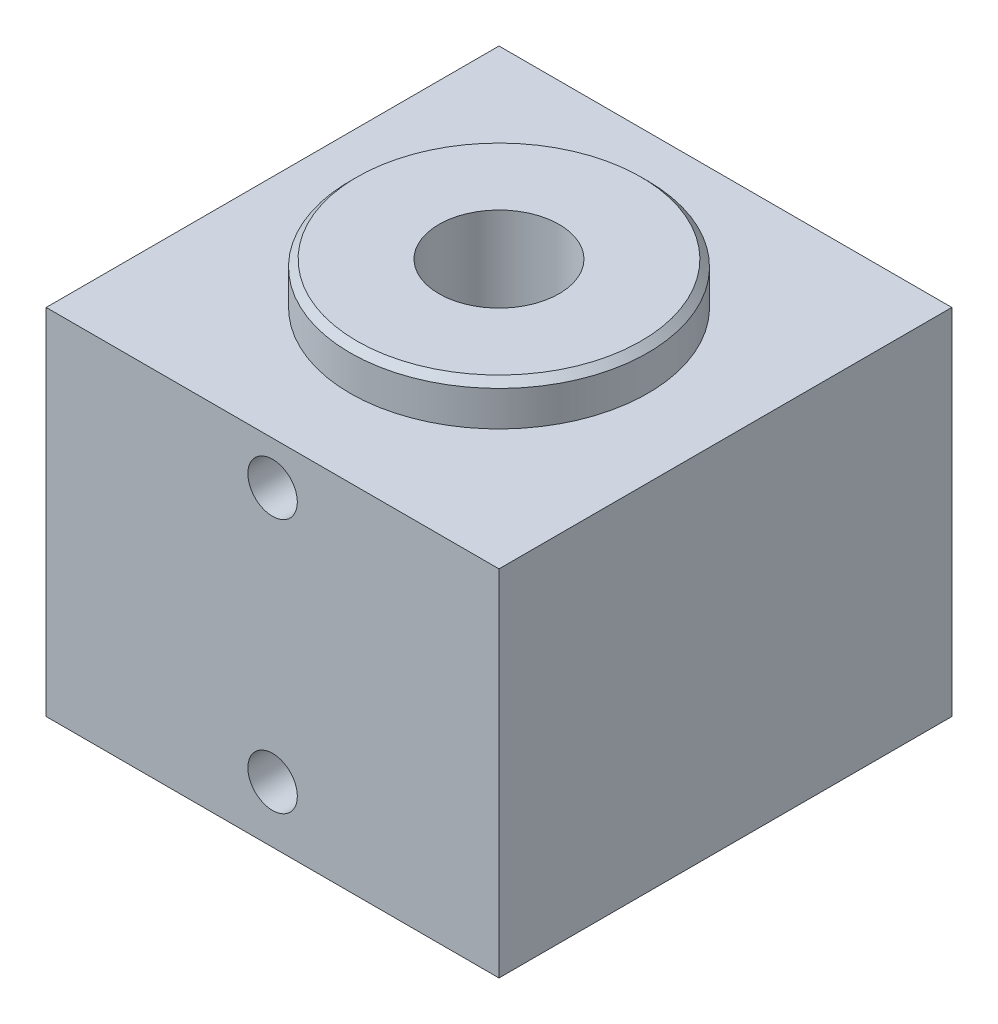
SolidWorks part; units mm, degrees
material "Alloy Steel"
ref_plane "Front Plane" through (0, 0, 0) normal (0, 0, 1) x (1, 0, 0)
ref_plane "Top Plane" through (0, 0, 0) normal (0, 1, 0) x (1, 0, 0)
ref_plane "Right Plane" through (0, 0, 0) normal (1, 0, 0) x (0, 0, -1)
sketch "Sketch1" plane through (0, 0, 0) normal (0, 1, 0) x (1, 0, 0)
  line L0 (-50.8, -50.8) -> (50.8, -50.8)
  line L1 (50.8, -50.8) -> (50.8, 50.8)
  line L2 (50.8, 50.8) -> (-50.8, 50.8)
  line L3 (-50.8, 50.8) -> (-50.8, -50.8)
  line L4 (-55.88, 0) -> (55.88, 0) construction
  line L5 (0, 0.7573) -> (0, -54.4639) construction
  dimension "D1" = 101.6
  dimension "D2" = 50.8
  dimension "D3" = 101.6
extrude "Extrude1" add sketch "Sketch1" along normal blind 79.502
sketch "Sketch2" plane through (0, 79.502, 0) normal (0, 1, 0) x (-1, 0, 0)
  circle A0 centre (0, 0) radius 33.401
  dimension "D1" = 66.802
extrude "Extrude2" add sketch "Sketch2" along normal blind 9.398
chamfer "Chamfer1" distance 1.524 angle 45 1 edges at (0, 88.9, 33.401)
sketch "Sketch3" plane through (0, 88.9, 0) normal (0, 1, 0) x (1, 0, 0)
  circle A0 centre (0, 0) radius 13.4874
  dimension "D1" = 26.9748
extrude "Cut-Extrude1" cut sketch "Sketch3" against normal through all
sketch "Sketch4" plane through (0, 0, 50.8) normal (0, 0, 1) x (1, 0, 0)
  line L0 (-50.8, 0) -> (50.8, 0) construction
  circle A0 centre (0, 69.85) radius 5.5499
  circle A1 centre (0, 12.7) radius 5.5499
  dimension "D1" = 11.0998
  dimension "D2" = 12.7
  dimension "D3" = 57.15
extrude "Cut-Extrude2" cut sketch "Sketch4" against normal blind 12.7
hole_wizard "Hole1" positions "Sketch6" profile "Sketch5" legacy
sketch "Sketch6" plane through (0, 0, 0) normal (0, -1, 0) x (1, 0, 0)
  line L0 (0, 0) -> (-63.1432, 0) construction
  line L1 (0, 0) -> (0, 58.5415) construction
  point P0 (-38.1, 38.1)
  point P9 (38.1, 38.1)
  point P11 (38.1, -38.1)
  point P12 (-38.1, -38.1)
  dimension "D1" = 76.2
  dimension "D2" = 76.2
sketch "Sketch5" plane through (-38.1, 0, 38.1) normal (1, 0, 0) x (0, 0, -1)
  line L0 (0, 0) -> (0, 12.7)
  line L1 (0, 12.7) -> (3.9688, 12.7)
  line L2 (3.9688, 12.7) -> (3.9688, 0)
  line L3 (3.9688, 0) -> (0, 0)
  line L4 (0, 110) -> (0, -10) construction
  dimension "Diameter" = 7.9375
  dimension "Depth" = 12.7
